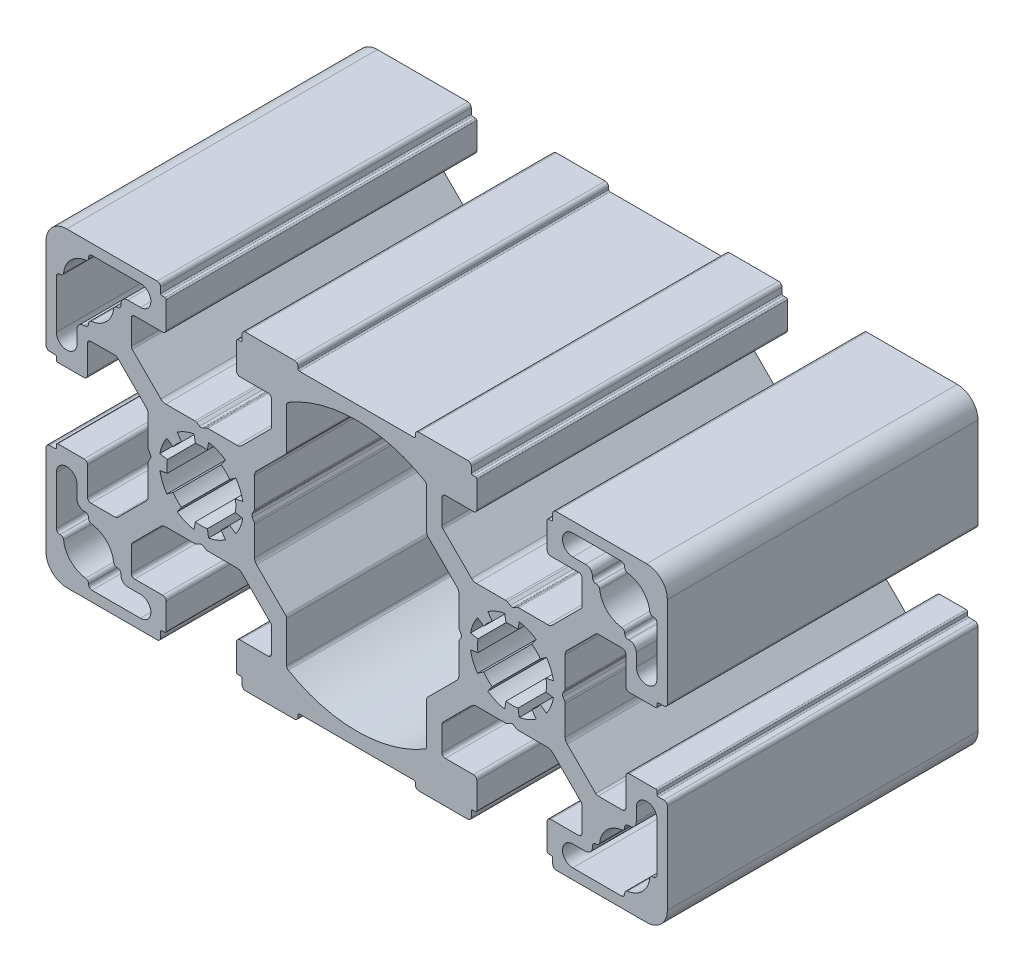
SolidWorks part; units mm, degrees
material "АД31Т ГОСТ 4784-97"
ref_plane "Спереди" through (0, 0, 0) normal (0, 0, 1) x (1, 0, 0)
ref_plane "Сверху" through (0, 0, 0) normal (0, 1, 0) x (1, 0, 0)
ref_plane "Справа" through (0, 0, 0) normal (1, 0, 0) x (0, 0, -1)
sketch "Эскиз1" plane through (0, 0, 0) normal (0, 0, 1) x (1, 0, 0)
  line L0 (-48.4414, 51.0481) -> (-48.4414, 44.0311)
  line L1 (-43.2664, 14.2231) -> (-36.2493, 14.2231)
  line L2 (-35.1419, 36.1522) -> (-35.1419, 40.3881)
  line L3 (-21.8414, 51.7231) -> (-17.7914, 51.7231)
  line L4 (-15.0914, 49.4623) -> (-15.0914, 45.6589)
  line L5 (-17.2012, 43.3419) -> (-15.2378, 45.3054)
  line L6 (-34.8271, 34.9731) -> (-35.0594, 34.5709)
  line L7 (-30.3093, 39.3189) -> (-30.9402, 40.2199)
  line L8 (-43.9414, 40.8231) -> (-43.9414, 44.8731)
  line L9 (-43.4414, 45.3731) -> (-39.9198, 45.3731)
  line L10 (-49.4414, 41.1231) -> (-48.6414, 41.1231)
  line L11 (-48.2414, 40.3231) -> (-44.4414, 40.3231)
  line L12 (-48.4414, 40.9231) -> (-48.4414, 40.5231)
  line L13 (-49.4414, 41.1231) -> (-48.6414, 41.1231)
  line L14 (-23.3456, 38.091) -> (-22.4445, 38.7219)
  line L15 (-23.3456, 38.091) -> (-22.4445, 38.7219)
  line L16 (-48.4414, 40.9231) -> (-48.4414, 40.5231)
  line L17 (-35.5602, 45.4633) -> (-33.3134, 43.2165)
  line L18 (-26.5123, 42.9236) -> (-22.2764, 42.9236)
  line L19 (-49.9414, 41.6231) -> (-49.9414, 54.7231)
  line L20 (-17.2914, 51.2231) -> (-17.2914, 47.7015)
  line L21 (-27.1914, 42.6089) -> (-26.7623, 42.8566)
  line L22 (11.9586, 18.7231) -> (7.9086, 18.7231)
  line L23 (-33.8414, 57.7231) -> (-46.9414, 57.7231)
  line L24 (-21.0414, 57.7231) -> (-13.9414, 57.7231)
  line L25 (-37.6815, 43.3419) -> (-39.5662, 45.2267)
  line L26 (-33.1414, 56.2231) -> (-32.7414, 56.2231)
  line L27 (-34.8271, 35.4731) -> (-35.0749, 35.9022)
  line L28 (-27.6914, 42.6089) -> (-28.1205, 42.8566)
  line L29 (-33.3414, 57.2231) -> (-33.3414, 56.4231)
  line L30 (-33.1414, 56.2231) -> (-32.7414, 56.2231)
  line L31 (-32.5414, 56.0231) -> (-32.5414, 52.2231)
  line L32 (-33.3414, 57.2231) -> (-33.3414, 56.4231)
  line L33 (-35.5602, 45.4633) -> (-37.4449, 47.348)
  line L34 (-33.0414, 51.7231) -> (-37.0914, 51.7231)
  line L35 (-37.6815, 43.3419) -> (-35.4347, 41.0952)
  line L36 (3.3586, 56.7231) -> (-13.2414, 56.7231)
  line L37 (-39.6466, 51.5481) -> (-39.5914, 51.5481)
  line L38 (-47.8861, 51.5481) -> (-47.9414, 51.5481)
  line L39 (-13.4414, 56.9231) -> (-13.4414, 57.2231)
  line L40 (-39.0914, 52.0481) -> (-39.0914, 52.2231)
  line L41 (-45.4414, 45.8731) -> (-45.4414, 44.0311)
  line L42 (-44.2664, 46.8731) -> (-44.4414, 46.8731)
  line L43 (-15.0914, 51.5901) -> (-15.0914, 49.4623)
  line L44 (-43.7664, 47.4284) -> (-43.7664, 47.3731)
  line L45 (38.5586, 19.3981) -> (38.5586, 26.4152)
  line L46 (-17.2012, 43.3419) -> (-19.448, 41.0952)
  line L47 (-27.1914, 42.6089) -> (-26.7891, 42.8411)
  line L48 (-28.3705, 42.9236) -> (-32.6063, 42.9236)
  line L49 (-21.8414, 51.7231) -> (-17.7914, 51.7231)
  line L50 (-19.3226, 45.4633) -> (-17.4378, 47.348)
  line L51 (-21.5414, 57.2231) -> (-21.5414, 56.4231)
  line L52 (-22.3414, 56.0231) -> (-22.3414, 52.2231)
  line L53 (-28.3705, 27.5226) -> (-32.6063, 27.5226)
  line L54 (-21.7414, 56.2231) -> (-22.1414, 56.2231)
  line L55 (-21.5414, 57.2231) -> (-21.5414, 56.4231)
  line L56 (-27.6914, 27.8374) -> (-28.1205, 27.5896)
  line L57 (-21.7414, 56.2231) -> (-22.1414, 56.2231)
  line L58 (-21.7414, 14.2231) -> (-22.1414, 14.2231)
  line L59 (-21.5414, 13.2231) -> (-21.5414, 14.0231)
  line L60 (-21.7414, 14.2231) -> (-22.1414, 14.2231)
  line L61 (-37.5914, 51.2231) -> (-37.5914, 47.7015)
  line L62 (-19.3226, 45.4633) -> (-21.5693, 43.2165)
  line L63 (-27.1914, 27.8374) -> (-26.7623, 27.5896)
  line L64 (-22.3414, 14.4231) -> (-22.3414, 18.2231)
  line L65 (-27.6914, 27.8374) -> (-28.0936, 27.6051)
  line L66 (-21.5414, 13.2231) -> (-21.5414, 14.0231)
  line L67 (-19.3226, 24.983) -> (-17.4378, 23.0982)
  line L68 (-21.8414, 18.7231) -> (-17.7914, 18.7231)
  line L69 (5.2086, 20.9839) -> (5.2086, 24.7873)
  line L70 (7.4086, 19.2231) -> (7.4086, 22.7447)
  line L71 (11.1586, 12.7231) -> (4.0586, 12.7231)
  line L72 (-28.3705, 42.9236) -> (-32.6063, 42.9236)
  line L73 (-24.5735, 39.3189) -> (-23.9426, 40.2199)
  line L74 (-19.7409, 36.1522) -> (-19.7409, 40.3881)
  line L75 (-26.5123, 27.5226) -> (-22.2764, 27.5226)
  line L76 (3.5586, 13.5231) -> (3.5586, 13.2231)
  line L77 (-33.0414, 18.7231) -> (-37.0914, 18.7231)
  line L78 (-43.7664, 14.7784) -> (-43.7664, 14.7231)
  line L79 (-23.3456, 32.3552) -> (-22.4445, 31.7243)
  line L80 (-24.5735, 31.1274) -> (-23.9426, 30.2263)
  line L81 (-38.0914, 17.2231) -> (-36.2493, 17.2231)
  line L82 (-23.3456, 32.3552) -> (-22.4445, 31.7243)
  line L83 (-24.5735, 31.1274) -> (-23.9426, 30.2263)
  line L84 (-26.5731, 30.2991) -> (-26.3821, 29.2158)
  line L85 (-26.5731, 30.2991) -> (-26.3821, 29.2158)
  line L86 (-28.3096, 30.2991) -> (-28.5006, 29.2158)
  line L87 (-31.5371, 32.3552) -> (-32.4382, 31.7243)
  line L88 (-28.3096, 30.2991) -> (-28.5006, 29.2158)
  line L89 (-31.5371, 32.3552) -> (-32.4382, 31.7243)
  line L90 (5.2086, 18.8562) -> (5.2086, 20.9839)
  line L91 (-24.5735, 31.1274) -> (-23.9426, 30.2263)
  line L92 (-28.3705, 27.5226) -> (-32.6063, 27.5226)
  line L93 (-17.2914, 19.2231) -> (-17.2914, 22.7447)
  line L94 (-17.2012, 27.1043) -> (-15.2378, 25.1409)
  line L95 (-15.0914, 20.9839) -> (-15.0914, 24.7873)
  line L96 (-21.8414, 18.7231) -> (-17.7914, 18.7231)
  line L97 (20.4265, 31.1274) -> (21.0574, 30.2263)
  line L98 (34.0586, 29.6231) -> (34.0586, 25.5731)
  line L99 (-19.3226, 24.983) -> (-21.5693, 27.2297)
  line L100 (-34.8271, 34.9731) -> (-35.0749, 34.544)
  line L101 (-37.5914, 19.2231) -> (-37.5914, 22.7447)
  line L102 (20.4265, 31.1274) -> (21.0574, 30.2263)
  line L103 (33.5586, 25.0731) -> (30.0371, 25.0731)
  line L104 (-17.2012, 27.1043) -> (-15.3165, 25.2196)
  line L105 (39.5586, 29.3231) -> (38.7586, 29.3231)
  line L106 (-19.7409, 34.294) -> (-19.7409, 30.0582)
  line L107 (38.3586, 30.1231) -> (34.5586, 30.1231)
  line L108 (38.5586, 29.5231) -> (38.5586, 29.9231)
  line L109 (-20.0556, 35.4731) -> (-19.8234, 35.8754)
  line L110 (39.5586, 29.3231) -> (38.7586, 29.3231)
  line L111 (13.4629, 32.3552) -> (12.5618, 31.7243)
  line L112 (-35.1419, 34.294) -> (-35.1419, 30.0582)
  line L113 (13.4629, 32.3552) -> (12.5618, 31.7243)
  line L114 (13.4629, 32.3552) -> (12.5618, 31.7243)
  line L115 (-28.3705, 27.5226) -> (-32.6063, 27.5226)
  line L116 (-27.1914, 27.8374) -> (-26.7891, 27.6051)
  line L117 (-17.2012, 27.1043) -> (-19.448, 29.3511)
  line L118 (38.5586, 29.5231) -> (38.5586, 29.9231)
  line L119 (-43.7664, 23.0179) -> (-43.7664, 23.0731)
  line L120 (-20.0556, 34.9731) -> (-19.8079, 34.544)
  line L121 (25.6774, 24.983) -> (23.4307, 27.2297)
  line L122 (-44.2664, 23.5731) -> (-44.4414, 23.5731)
  line L123 (-45.4414, 24.5731) -> (-45.4414, 26.4152)
  line L124 (-39.0914, 18.3981) -> (-39.0914, 18.2231)
  line L125 (9.8581, 36.1522) -> (9.8581, 40.3881)
  line L126 (-47.8861, 18.8981) -> (-47.9414, 18.8981)
  line L127 (-31.5371, 38.091) -> (-32.4382, 38.7219)
  line L128 (-28.3096, 40.1472) -> (-28.5006, 41.2304)
  line L129 (-26.5731, 40.1472) -> (-26.3821, 41.2304)
  line L130 (-38.0914, 53.2231) -> (-36.2493, 53.2231)
  line L131 (-32.3654, 34.3549) -> (-33.4487, 34.1639)
  line L132 (-32.3654, 36.0914) -> (-33.4487, 36.2824)
  line L133 (-26.5731, 30.2991) -> (-26.3821, 29.2158)
  line L134 (-28.3096, 30.2991) -> (-28.5006, 29.2158)
  line L135 (-30.3093, 31.1274) -> (-30.9402, 30.2263)
  line L136 (-31.5371, 32.3552) -> (-32.4382, 31.7243)
  line L137 (-32.3654, 34.3549) -> (-33.4487, 34.1639)
  line L138 (-32.3654, 36.0914) -> (-33.4487, 36.2824)
  line L139 (-24.5735, 39.3189) -> (-23.9426, 40.2199)
  line L140 (-23.3456, 38.091) -> (-22.4445, 38.7219)
  line L141 (-22.5173, 36.0914) -> (-21.434, 36.2824)
  line L142 (-22.5173, 34.3549) -> (-21.434, 34.1639)
  line L143 (-23.3456, 32.3552) -> (-22.4445, 31.7243)
  line L144 (-24.5735, 31.1274) -> (-23.9426, 30.2263)
  line L145 (-43.7664, 55.6679) -> (-43.7664, 55.7231)
  line L146 (-39.6466, 18.8981) -> (-39.5914, 18.8981)
  line L147 (-33.0414, 51.7231) -> (-37.0914, 51.7231)
  line L148 (-43.2664, 56.2231) -> (-36.2493, 56.2231)
  line L149 (16.6295, 27.5226) -> (12.3937, 27.5226)
  line L150 (-37.6815, 27.1043) -> (-35.4347, 29.3511)
  line L151 (-33.0414, 18.7231) -> (-37.0914, 18.7231)
  line L152 (-35.5602, 24.983) -> (-37.4449, 23.0982)
  line L153 (-33.3414, 13.2231) -> (-33.3414, 14.0231)
  line L154 (-32.5414, 14.4231) -> (-32.5414, 18.2231)
  line L155 (-33.1414, 14.2231) -> (-32.7414, 14.2231)
  line L156 (-33.3414, 13.2231) -> (-33.3414, 14.0231)
  line L157 (-27.6914, 27.8374) -> (-28.1205, 27.5896)
  line L158 (-33.1414, 14.2231) -> (-32.7414, 14.2231)
  line L159 (-37.6815, 27.1043) -> (-39.5662, 25.2196)
  line L160 (40.0586, 28.8231) -> (40.0586, 15.7231)
  line L161 (-33.8414, 12.7231) -> (-46.9414, 12.7231)
  line L162 (10.1729, 35.4731) -> (9.9251, 35.9022)
  line L163 (-27.1914, 27.8374) -> (-26.7623, 27.5896)
  line L164 (17.3086, 27.8374) -> (16.8795, 27.5896)
  line L165 (-20.0556, 35.4731) -> (-19.8079, 35.9022)
  line L166 (-49.9414, 28.8231) -> (-49.9414, 15.7231)
  line L167 (-26.5123, 27.5226) -> (-22.2764, 27.5226)
  line L168 (-19.7409, 36.1522) -> (-19.7409, 40.3881)
  line L169 (-35.5602, 24.983) -> (-33.3134, 27.2297)
  line L170 (-48.4414, 29.5231) -> (-48.4414, 29.9231)
  line L171 (-23.3456, 32.3552) -> (-22.4445, 31.7243)
  line L172 (-23.3456, 32.3552) -> (-22.4445, 31.7243)
  line L173 (-23.3456, 32.3552) -> (-22.4445, 31.7243)
  line L174 (-49.4414, 29.3231) -> (-48.6414, 29.3231)
  line L175 (-48.4414, 29.5231) -> (-48.4414, 29.9231)
  line L176 (-48.2414, 30.1231) -> (-44.4414, 30.1231)
  line L177 (-49.4414, 29.3231) -> (-48.6414, 29.3231)
  line L178 (-43.4414, 25.0731) -> (-39.9198, 25.0731)
  line L179 (-30.3093, 31.1274) -> (-30.9402, 30.2263)
  line L180 (-43.9414, 29.6231) -> (-43.9414, 25.5731)
  line L181 (-30.3093, 31.1274) -> (-30.9402, 30.2263)
  line L182 (23.9586, 12.7231) -> (37.0586, 12.7231)
  line L183 (27.7988, 27.1043) -> (29.6835, 25.2196)
  line L184 (23.2586, 14.2231) -> (22.8586, 14.2231)
  line L185 (17.8086, 27.8374) -> (18.2377, 27.5896)
  line L186 (-48.4414, 19.3981) -> (-48.4414, 26.4152)
  line L187 (23.4586, 13.2231) -> (23.4586, 14.0231)
  line L188 (23.2586, 14.2231) -> (22.8586, 14.2231)
  line L189 (22.6586, 14.4231) -> (22.6586, 18.2231)
  line L190 (23.4586, 13.2231) -> (23.4586, 14.0231)
  line L191 (25.6774, 24.983) -> (27.5622, 23.0982)
  line L192 (23.1586, 18.7231) -> (27.2086, 18.7231)
  line L193 (27.7988, 27.1043) -> (25.552, 29.3511)
  line L194 (33.3836, 56.2231) -> (26.3666, 56.2231)
  line L195 (23.1586, 51.7231) -> (27.2086, 51.7231)
  line L196 (29.7639, 18.8981) -> (29.7086, 18.8981)
  line L197 (33.8836, 55.6679) -> (33.8836, 55.7231)
  line L198 (14.6907, 31.1274) -> (14.0598, 30.2263)
  line L199 (13.4629, 32.3552) -> (12.5618, 31.7243)
  line L200 (12.6346, 34.3549) -> (11.5513, 34.1639)
  line L201 (12.6346, 36.0914) -> (11.5513, 36.2824)
  line L202 (13.4629, 38.091) -> (12.5618, 38.7219)
  line L203 (14.6907, 39.3189) -> (14.0598, 40.2199)
  line L204 (22.4827, 36.0914) -> (23.566, 36.2824)
  line L205 (22.4827, 34.3549) -> (23.566, 34.1639)
  line L206 (21.6544, 32.3552) -> (22.5555, 31.7243)
  line L207 (20.4265, 31.1274) -> (21.0574, 30.2263)
  line L208 (18.4269, 30.2991) -> (18.6179, 29.2158)
  line L209 (16.6904, 30.2991) -> (16.4994, 29.2158)
  line L210 (22.4827, 36.0914) -> (23.566, 36.2824)
  line L211 (22.4827, 34.3549) -> (23.566, 34.1639)
  line L212 (28.2086, 53.2231) -> (26.3666, 53.2231)
  line L213 (16.6904, 40.1472) -> (16.4994, 41.2304)
  line L214 (18.4269, 40.1472) -> (18.6179, 41.2304)
  line L215 (21.6544, 38.091) -> (22.5555, 38.7219)
  line L216 (38.0034, 18.8981) -> (38.0586, 18.8981)
  line L217 (29.2086, 18.3981) -> (29.2086, 18.2231)
  line L218 (35.5586, 24.5731) -> (35.5586, 26.4152)
  line L219 (34.3836, 23.5731) -> (34.5586, 23.5731)
  line L220 (10.1729, 34.9731) -> (9.9251, 34.544)
  line L221 (33.8836, 23.0179) -> (33.8836, 23.0731)
  line L222 (7.3185, 27.1043) -> (9.5653, 29.3511)
  line L223 (17.3086, 27.8374) -> (16.9064, 27.6051)
  line L224 (18.4877, 27.5226) -> (22.7236, 27.5226)
  line L225 (25.2591, 34.294) -> (25.2591, 30.0582)
  line L226 (10.1729, 35.4731) -> (9.9406, 35.8754)
  line L227 (9.8581, 34.294) -> (9.8581, 30.0582)
  line L228 (7.3185, 27.1043) -> (5.4338, 25.2196)
  line L229 (27.7086, 19.2231) -> (27.7086, 22.7447)
  line L230 (24.9444, 34.9731) -> (25.1921, 34.544)
  line L231 (9.4398, 24.983) -> (11.6866, 27.2297)
  line L232 (11.9586, 18.7231) -> (7.9086, 18.7231)
  line L233 (5.2086, 20.9839) -> (5.2086, 24.7873)
  line L234 (7.3185, 27.1043) -> (5.3551, 25.1409)
  line L235 (7.4086, 19.2231) -> (7.4086, 22.7447)
  line L236 (18.4877, 27.5226) -> (22.7236, 27.5226)
  line L237 (14.6907, 31.1274) -> (14.0598, 30.2263)
  line L238 (21.6544, 32.3552) -> (22.5555, 31.7243)
  line L239 (18.4269, 30.2991) -> (18.6179, 29.2158)
  line L240 (21.6544, 32.3552) -> (22.5555, 31.7243)
  line L241 (18.4269, 30.2991) -> (18.6179, 29.2158)
  line L242 (16.6904, 30.2991) -> (16.4994, 29.2158)
  line L243 (16.6904, 30.2991) -> (16.4994, 29.2158)
  line L244 (14.6907, 31.1274) -> (14.0598, 30.2263)
  line L245 (13.4629, 32.3552) -> (12.5618, 31.7243)
  line L246 (28.2086, 17.2231) -> (26.3666, 17.2231)
  line L247 (14.6907, 31.1274) -> (14.0598, 30.2263)
  line L248 (13.4629, 32.3552) -> (12.5618, 31.7243)
  line L249 (33.8836, 14.7784) -> (33.8836, 14.7231)
  line L250 (23.1586, 18.7231) -> (27.2086, 18.7231)
  line L251 (11.9586, 18.7231) -> (7.9086, 18.7231)
  line L252 (16.6295, 27.5226) -> (12.3937, 27.5226)
  line L253 (9.8581, 36.1522) -> (9.8581, 40.3881)
  line L254 (14.6907, 39.3189) -> (14.0598, 40.2199)
  line L255 (18.4877, 42.9236) -> (22.7236, 42.9236)
  line L256 (9.4398, 24.983) -> (7.5551, 23.0982)
  line L257 (11.6586, 13.2231) -> (11.6586, 14.0231)
  line L258 (11.9586, 18.7231) -> (7.9086, 18.7231)
  line L259 (9.4398, 24.983) -> (7.5551, 23.0982)
  line L260 (11.6586, 13.2231) -> (11.6586, 14.0231)
  line L261 (17.8086, 27.8374) -> (18.2109, 27.6051)
  line L262 (12.4586, 14.4231) -> (12.4586, 18.2231)
  line L263 (17.3086, 27.8374) -> (16.8795, 27.5896)
  line L264 (9.4398, 45.4633) -> (11.6866, 43.2165)
  line L265 (27.7086, 51.2231) -> (27.7086, 47.7015)
  line L266 (11.8586, 14.2231) -> (12.2586, 14.2231)
  line L267 (11.6586, 13.2231) -> (11.6586, 14.0231)
  line L268 (11.8586, 14.2231) -> (12.2586, 14.2231)
  line L269 (11.8586, 56.2231) -> (12.2586, 56.2231)
  line L270 (17.8086, 27.8374) -> (18.2377, 27.5896)
  line L271 (11.6586, 57.2231) -> (11.6586, 56.4231)
  line L272 (11.8586, 56.2231) -> (12.2586, 56.2231)
  line L273 (18.4877, 27.5226) -> (22.7236, 27.5226)
  line L274 (12.4586, 56.0231) -> (12.4586, 52.2231)
  line L275 (11.6586, 57.2231) -> (11.6586, 56.4231)
  line L276 (9.4398, 45.4633) -> (7.5551, 47.348)
  line L277 (11.9586, 51.7231) -> (7.9086, 51.7231)
  line L278 (18.4877, 42.9236) -> (22.7236, 42.9236)
  line L279 (17.3086, 42.6089) -> (16.9064, 42.8411)
  line L280 (7.3185, 43.3419) -> (9.5653, 41.0952)
  line L281 (33.8836, 47.4284) -> (33.8836, 47.3731)
  line L282 (5.2086, 51.5901) -> (5.2086, 49.4623)
  line L283 (34.3836, 46.8731) -> (34.5586, 46.8731)
  line L284 (35.5586, 45.8731) -> (35.5586, 44.0311)
  line L285 (29.2086, 52.0481) -> (29.2086, 52.2231)
  line L286 (3.5586, 56.9231) -> (3.5586, 57.2231)
  line L287 (38.0034, 51.5481) -> (38.0586, 51.5481)
  line L288 (29.7639, 51.5481) -> (29.7086, 51.5481)
  line L289 (27.7988, 43.3419) -> (25.552, 41.0952)
  line L290 (23.1586, 51.7231) -> (27.2086, 51.7231)
  line L291 (25.6774, 45.4633) -> (27.5622, 47.348)
  line L292 (23.4586, 57.2231) -> (23.4586, 56.4231)
  line L293 (22.6586, 56.0231) -> (22.6586, 52.2231)
  line L294 (23.2586, 56.2231) -> (22.8586, 56.2231)
  line L295 (23.4586, 57.2231) -> (23.4586, 56.4231)
  line L296 (17.8086, 42.6089) -> (18.2377, 42.8566)
  line L297 (24.9444, 35.4731) -> (25.1921, 35.9022)
  line L298 (23.2586, 56.2231) -> (22.8586, 56.2231)
  line L299 (27.7988, 43.3419) -> (29.6835, 45.2267)
  line L300 (11.1586, 57.7231) -> (4.0586, 57.7231)
  line L301 (23.9586, 57.7231) -> (37.0586, 57.7231)
  line L302 (17.3086, 42.6089) -> (16.8795, 42.8566)
  line L303 (7.4086, 51.2231) -> (7.4086, 47.7015)
  line L304 (40.0586, 41.6231) -> (40.0586, 54.7231)
  line L305 (16.6295, 42.9236) -> (12.3937, 42.9236)
  line L306 (25.6774, 45.4633) -> (23.4307, 43.2165)
  line L307 (38.5586, 40.9231) -> (38.5586, 40.5231)
  line L308 (13.4629, 38.091) -> (12.5618, 38.7219)
  line L309 (13.4629, 38.091) -> (12.5618, 38.7219)
  line L310 (39.5586, 41.1231) -> (38.7586, 41.1231)
  line L311 (38.5586, 40.9231) -> (38.5586, 40.5231)
  line L312 (38.3586, 40.3231) -> (34.5586, 40.3231)
  line L313 (39.5586, 41.1231) -> (38.7586, 41.1231)
  line L314 (33.5586, 45.3731) -> (30.0371, 45.3731)
  line L315 (34.0586, 40.8231) -> (34.0586, 44.8731)
  line L316 (20.4265, 39.3189) -> (21.0574, 40.2199)
  line L317 (24.9444, 34.9731) -> (25.1766, 34.5709)
  line L318 (7.3185, 43.3419) -> (5.3551, 45.3054)
  line L319 (5.2086, 49.4623) -> (5.2086, 45.6589)
  line L320 (11.9586, 51.7231) -> (7.9086, 51.7231)
  line L321 (25.2591, 36.1522) -> (25.2591, 40.3881)
  line L322 (33.3836, 14.2231) -> (26.3666, 14.2231)
  line L323 (38.5586, 51.0481) -> (38.5586, 44.0311)
  line L325 (12.4586, 14.4231) -> (12.4586, 18.2231)
  line L326 (11.8586, 14.2231) -> (12.2586, 14.2231)
  line L327 (11.6586, 13.2231) -> (11.6586, 14.0231)
  line L328 (11.8586, 14.2231) -> (12.2586, 14.2231)
  line L329 (-21.7414, 14.2231) -> (-22.1414, 14.2231)
  line L330 (-21.5414, 13.2231) -> (-21.5414, 14.0231)
  line L331 (-21.7414, 14.2231) -> (-22.1414, 14.2231)
  line L332 (-22.3414, 14.4231) -> (-22.3414, 18.2231)
  line L333 (-21.5414, 13.2231) -> (-21.5414, 14.0231)
  line L334 (-19.3226, 24.983) -> (-17.4378, 23.0982)
  line L335 (-21.8414, 18.7231) -> (-17.7914, 18.7231)
  line L336 (-15.0914, 18.8562) -> (-15.0914, 20.9839)
  line L337 (-13.4414, 13.5231) -> (-13.4414, 13.2231)
  line L338 (3.3586, 13.7231) -> (-13.2414, 13.7231)
  line L339 (-21.0414, 12.7231) -> (-13.9414, 12.7231)
  line L340 (-17.2914, 19.2231) -> (-17.2914, 22.7447)
  line L341 (-15.0914, 20.9839) -> (-15.0914, 24.7873)
  line L342 (-21.8414, 18.7231) -> (-17.7914, 18.7231)
  arc A0 (-30.3093, 39.3189) -> (-31.5371, 38.091) centre (-27.4414, 35.2231) ccw
  arc A1 (-32.4382, 38.7219) -> (-33.4487, 36.2824) centre (-27.4414, 35.2231) ccw
  arc A2 (-46.9414, 57.7231) -> (-49.9414, 54.7231) centre (-46.9414, 54.7231) ccw
  arc A3 (-39.5662, 45.2267) -> (-39.9198, 45.3731) centre (-39.9198, 44.8731) ccw
  arc A4 (-43.4414, 45.3731) -> (-43.9414, 44.8731) centre (-43.4414, 44.8731) ccw
  arc A5 (-44.4414, 40.3231) -> (-43.9414, 40.8231) centre (-44.4414, 40.8231) ccw
  arc A6 (-49.9414, 41.6231) -> (-49.4414, 41.1231) centre (-49.4414, 41.6231) ccw
  arc A7 (-48.2414, 40.3231) -> (-48.4414, 40.5231) centre (-48.2414, 40.5231) cw
  arc A8 (-48.6414, 41.1231) -> (-48.4414, 40.9231) centre (-48.6414, 40.9231) cw
  arc A9 (-35.4347, 41.0952) -> (-35.1419, 40.3881) centre (-36.1419, 40.3881) cw
  arc A10 (-17.2914, 51.2231) -> (-17.7914, 51.7231) centre (-17.7914, 51.2231) ccw
  arc A11 (-15.2378, 45.3054) -> (-15.0914, 45.6589) centre (-15.5914, 45.6589) ccw
  arc A12 (4.9626, 52.0208) -> (5.2086, 51.5901) centre (4.7086, 51.5901) cw
  arc A13 (-13.4414, 57.2231) -> (-13.9414, 57.7231) centre (-13.9414, 57.2231) ccw
  arc A14 (-13.2414, 56.7231) -> (-13.4414, 56.9231) centre (-13.2414, 56.9231) cw
  arc A15 (-21.5414, 14.0231) -> (-21.7414, 14.2231) centre (-21.7414, 14.0231) ccw
  arc A16 (-35.0749, 34.544) -> (-35.1419, 34.294) centre (-34.6419, 34.294) ccw
  arc A17 (-33.3414, 56.4231) -> (-33.1414, 56.2231) centre (-33.1414, 56.4231) ccw
  arc A18 (-34.8271, 34.9731) -> (-34.8271, 35.4731) centre (-35.2601, 35.2231) ccw
  arc A19 (-49.9414, 41.6231) -> (-49.4414, 41.1231) centre (-49.4414, 41.6231) ccw
  arc A20 (-48.6414, 41.1231) -> (-48.4414, 40.9231) centre (-48.6414, 40.9231) cw
  arc A21 (-33.8414, 57.7231) -> (-33.3414, 57.2231) centre (-33.8414, 57.2231) cw
  arc A22 (-28.1205, 42.8566) -> (-28.3705, 42.9236) centre (-28.3705, 42.4236) ccw
  arc A23 (-21.0414, 12.7231) -> (-21.5414, 13.2231) centre (-21.0414, 13.2231) cw
  arc A24 (-27.1914, 42.6089) -> (-27.6914, 42.6089) centre (-27.4414, 43.0419) cw
  arc A25 (-33.3414, 56.4231) -> (-33.1414, 56.2231) centre (-33.1414, 56.4231) ccw
  arc A26 (-32.5414, 56.0231) -> (-32.7414, 56.2231) centre (-32.7414, 56.0231) ccw
  arc A27 (-33.8414, 57.7231) -> (-33.3414, 57.2231) centre (-33.8414, 57.2231) cw
  arc A28 (-32.5414, 52.2231) -> (-33.0414, 51.7231) centre (-33.0414, 52.2231) cw
  arc A29 (-37.5914, 51.2231) -> (-37.0914, 51.7231) centre (-37.0914, 51.2231) cw
  arc A30 (-33.3134, 43.2165) -> (-32.6063, 42.9236) centre (-32.6063, 43.9236) ccw
  arc A31 (-43.3266, 47.9247) -> (-40.143, 51.1084) centre (-43.7664, 51.5481) ccw
  arc A32 (-48.4414, 44.0311) -> (-45.4414, 44.0311) centre (-46.9414, 44.0311) ccw
  arc A33 (-44.4414, 46.8731) -> (-45.4414, 45.8731) centre (-44.4414, 45.8731) ccw
  arc A34 (-47.9414, 51.5481) -> (-48.4414, 51.0481) centre (-47.9414, 51.0481) ccw
  arc A35 (-47.8861, 51.5481) -> (-47.3898, 51.9879) centre (-47.8861, 52.0481) ccw
  arc A36 (-43.7664, 47.4284) -> (-43.3266, 47.9247) centre (-43.2664, 47.4284) cw
  arc A37 (-21.5414, 14.0231) -> (-21.7414, 14.2231) centre (-21.7414, 14.0231) ccw
  arc A38 (-22.3414, 14.4231) -> (-22.1414, 14.2231) centre (-22.1414, 14.4231) ccw
  arc A39 (-21.0414, 12.7231) -> (-21.5414, 13.2231) centre (-21.0414, 13.2231) cw
  arc A40 (-17.4378, 47.348) -> (-17.2914, 47.7015) centre (-17.7914, 47.7015) ccw
  arc A41 (-22.3414, 18.2231) -> (-21.8414, 18.7231) centre (-21.8414, 18.2231) cw
  arc A42 (-17.2914, 19.2231) -> (-17.7914, 18.7231) centre (-17.7914, 19.2231) cw
  arc A43 (-26.7623, 42.8566) -> (-26.5123, 42.9236) centre (-26.5123, 42.4236) cw
  arc A44 (-37.4449, 47.348) -> (-37.5914, 47.7015) centre (-37.0914, 47.7015) cw
  arc A45 (-17.4378, 23.0982) -> (-17.2914, 22.7447) centre (-17.7914, 22.7447) cw
  arc A46 (4.9626, 18.4254) -> (-14.8453, 18.4254) centre (-4.9414, 35.2231) cw
  arc A47 (7.4086, 19.2231) -> (7.9086, 18.7231) centre (7.9086, 19.2231) ccw
  arc A48 (-26.7623, 27.5896) -> (-26.5123, 27.5226) centre (-26.5123, 28.0226) ccw
  arc A49 (5.3551, 25.1409) -> (5.2086, 24.7873) centre (5.7086, 24.7873) ccw
  arc A50 (-21.5693, 43.2165) -> (-22.2764, 42.9236) centre (-22.2764, 43.9236) cw
  arc A51 (-27.6914, 27.8374) -> (-27.1914, 27.8374) centre (-27.4414, 27.4044) cw
  arc A52 (-17.2914, 51.2231) -> (-17.7914, 51.7231) centre (-17.7914, 51.2231) ccw
  arc A53 (-22.3414, 52.2231) -> (-21.8414, 51.7231) centre (-21.8414, 52.2231) ccw
  arc A54 (-21.0414, 57.7231) -> (-21.5414, 57.2231) centre (-21.0414, 57.2231) ccw
  arc A55 (-22.3414, 56.0231) -> (-22.1414, 56.2231) centre (-22.1414, 56.0231) cw
  arc A56 (-21.5414, 56.4231) -> (-21.7414, 56.2231) centre (-21.7414, 56.4231) cw
  arc A57 (-21.0414, 57.7231) -> (-21.5414, 57.2231) centre (-21.0414, 57.2231) ccw
  arc A58 (-28.1205, 27.5896) -> (-28.3705, 27.5226) centre (-28.3705, 28.0226) cw
  arc A59 (-15.2378, 25.1409) -> (-15.0914, 24.7873) centre (-15.5914, 24.7873) cw
  arc A60 (-17.2914, 19.2231) -> (-17.7914, 18.7231) centre (-17.7914, 19.2231) cw
  arc A61 (-21.5414, 56.4231) -> (-21.7414, 56.2231) centre (-21.7414, 56.4231) cw
  arc A62 (-19.448, 41.0952) -> (-19.7409, 40.3881) centre (-18.7409, 40.3881) ccw
  arc A63 (20.4265, 31.1274) -> (21.6544, 32.3552) centre (17.5586, 35.2231) ccw
  arc A64 (37.0586, 12.7231) -> (40.0586, 15.7231) centre (37.0586, 15.7231) ccw
  arc A65 (29.6835, 25.2196) -> (30.0371, 25.0731) centre (30.0371, 25.5731) ccw
  arc A66 (33.5586, 25.0731) -> (34.0586, 25.5731) centre (33.5586, 25.5731) ccw
  arc A67 (-19.8079, 35.9022) -> (-19.7409, 36.1522) centre (-20.2409, 36.1522) ccw
  arc A68 (34.5586, 30.1231) -> (34.0586, 29.6231) centre (34.5586, 29.6231) ccw
  arc A69 (40.0586, 28.8231) -> (39.5586, 29.3231) centre (39.5586, 28.8231) ccw
  arc A70 (38.3586, 30.1231) -> (38.5586, 29.9231) centre (38.3586, 29.9231) cw
  arc A71 (-22.4445, 38.7219) -> (-21.434, 36.2824) centre (-27.4414, 35.2231) cw
  arc A72 (-20.0556, 35.4731) -> (-20.0556, 34.9731) centre (-19.6226, 35.2231) ccw
  arc A73 (-24.5735, 39.3189) -> (-23.3456, 38.091) centre (-27.4414, 35.2231) cw
  arc A74 (-37.5914, 19.2231) -> (-37.0914, 18.7231) centre (-37.0914, 19.2231) ccw
  arc A75 (-36.2493, 14.2231) -> (-36.2493, 17.2231) centre (-36.2493, 15.7231) ccw
  arc A76 (-39.0914, 18.2231) -> (-38.0914, 17.2231) centre (-38.0914, 18.2231) ccw
  arc A77 (-43.7664, 14.7231) -> (-43.2664, 14.2231) centre (-43.2664, 14.7231) ccw
  arc A78 (-43.7664, 14.7784) -> (-44.2061, 15.2747) centre (-44.2664, 14.7784) ccw
  arc A79 (-39.6466, 18.8981) -> (-40.143, 19.3379) centre (-39.6466, 19.3981) cw
  arc A80 (-39.5914, 18.8981) -> (-39.0914, 18.3981) centre (-39.5914, 18.3981) cw
  arc A81 (-44.2061, 15.2747) -> (-47.3898, 18.4584) centre (-43.7664, 18.8981) cw
  arc A82 (-43.7664, 23.0731) -> (-44.2664, 23.5731) centre (-44.2664, 23.0731) ccw
  arc A83 (-46.9414, 12.7231) -> (-49.9414, 15.7231) centre (-46.9414, 15.7231) cw
  arc A84 (-23.3456, 32.3552) -> (-24.5735, 31.1274) centre (-27.4414, 35.2231) cw
  arc A85 (-23.9426, 30.2263) -> (-26.3821, 29.2158) centre (-27.4414, 35.2231) cw
  arc A86 (-26.5731, 30.2991) -> (-28.3096, 30.2991) centre (-27.4414, 35.2231) cw
  arc A87 (-28.5006, 29.2158) -> (-30.9402, 30.2263) centre (-27.4414, 35.2231) cw
  arc A88 (-23.9426, 30.2263) -> (-26.3821, 29.2158) centre (-27.4414, 35.2231) cw
  arc A89 (-26.5731, 30.2991) -> (-28.3096, 30.2991) centre (-27.4414, 35.2231) cw
  arc A90 (-28.5006, 29.2158) -> (-30.9402, 30.2263) centre (-27.4414, 35.2231) cw
  arc A91 (-24.5735, 31.1274) -> (-23.3456, 32.3552) centre (-27.4414, 35.2231) ccw
  arc A92 (-19.8079, 34.544) -> (-19.7409, 34.294) centre (-20.2409, 34.294) cw
  arc A93 (38.7586, 29.3231) -> (38.5586, 29.5231) centre (38.7586, 29.5231) cw
  arc A94 (25.552, 29.3511) -> (25.2591, 30.0582) centre (26.2591, 30.0582) cw
  arc A95 (23.4586, 14.0231) -> (23.2586, 14.2231) centre (23.2586, 14.0231) ccw
  arc A96 (40.0586, 28.8231) -> (39.5586, 29.3231) centre (39.5586, 28.8231) ccw
  arc A97 (38.7586, 29.3231) -> (38.5586, 29.5231) centre (38.7586, 29.5231) cw
  arc A98 (23.9586, 12.7231) -> (23.4586, 13.2231) centre (23.9586, 13.2231) cw
  arc A99 (18.2377, 27.5896) -> (18.4877, 27.5226) centre (18.4877, 28.0226) ccw
  arc A100 (-19.448, 29.3511) -> (-19.7409, 30.0582) centre (-18.7409, 30.0582) cw
  arc A101 (17.3086, 27.8374) -> (17.8086, 27.8374) centre (17.5586, 27.4044) cw
  arc A102 (-35.0749, 35.9022) -> (-35.1419, 36.1522) centre (-34.6419, 36.1522) cw
  arc A103 (23.4586, 14.0231) -> (23.2586, 14.2231) centre (23.2586, 14.0231) ccw
  arc A104 (22.6586, 14.4231) -> (22.8586, 14.2231) centre (22.8586, 14.4231) ccw
  arc A105 (23.9586, 12.7231) -> (23.4586, 13.2231) centre (23.9586, 13.2231) cw
  arc A106 (22.6586, 18.2231) -> (23.1586, 18.7231) centre (23.1586, 18.2231) cw
  arc A107 (27.7086, 19.2231) -> (27.2086, 18.7231) centre (27.2086, 19.2231) cw
  arc A108 (23.4307, 27.2297) -> (22.7236, 27.5226) centre (22.7236, 26.5226) ccw
  arc A109 (33.4439, 22.5215) -> (30.2602, 19.3379) centre (33.8836, 18.8981) ccw
  arc A110 (38.5586, 26.4152) -> (35.5586, 26.4152) centre (37.0586, 26.4152) ccw
  arc A111 (-21.5693, 27.2297) -> (-22.2764, 27.5226) centre (-22.2764, 26.5226) ccw
  arc A112 (34.5586, 23.5731) -> (35.5586, 24.5731) centre (34.5586, 24.5731) ccw
  arc A113 (38.0586, 18.8981) -> (38.5586, 19.3981) centre (38.0586, 19.3981) ccw
  arc A114 (-28.5006, 41.2304) -> (-30.9402, 40.2199) centre (-27.4414, 35.2231) ccw
  arc A115 (-26.5731, 40.1472) -> (-28.3096, 40.1472) centre (-27.4414, 35.2231) ccw
  arc A116 (-23.9426, 40.2199) -> (-26.3821, 41.2304) centre (-27.4414, 35.2231) ccw
  arc A117 (-23.3456, 38.091) -> (-24.5735, 39.3189) centre (-27.4414, 35.2231) ccw
  arc A118 (-22.5173, 34.3549) -> (-22.5173, 36.0914) centre (-27.4414, 35.2231) ccw
  arc A119 (-21.434, 36.2824) -> (-22.4445, 38.7219) centre (-27.4414, 35.2231) ccw
  arc A120 (-24.5735, 31.1274) -> (-23.3456, 32.3552) centre (-27.4414, 35.2231) ccw
  arc A121 (-22.4445, 31.7243) -> (-21.434, 34.1639) centre (-27.4414, 35.2231) ccw
  arc A122 (-28.3096, 30.2991) -> (-26.5731, 30.2991) centre (-27.4414, 35.2231) ccw
  arc A123 (-26.3821, 29.2158) -> (-23.9426, 30.2263) centre (-27.4414, 35.2231) ccw
  arc A124 (-31.5371, 32.3552) -> (-30.3093, 31.1274) centre (-27.4414, 35.2231) ccw
  arc A125 (-30.9402, 30.2263) -> (-28.5006, 29.2158) centre (-27.4414, 35.2231) ccw
  arc A126 (-32.3654, 36.0914) -> (-32.3654, 34.3549) centre (-27.4414, 35.2231) ccw
  arc A127 (-33.4487, 34.1639) -> (-32.4382, 31.7243) centre (-27.4414, 35.2231) ccw
  arc A128 (-46.9414, 57.7231) -> (-49.9414, 54.7231) centre (-46.9414, 54.7231) ccw
  arc A129 (-43.7664, 47.3731) -> (-44.2664, 46.8731) centre (-44.2664, 47.3731) cw
  arc A130 (-44.2061, 55.1715) -> (-47.3898, 51.9879) centre (-43.7664, 51.5481) ccw
  arc A131 (-39.5914, 51.5481) -> (-39.0914, 52.0481) centre (-39.5914, 52.0481) ccw
  arc A132 (-39.6466, 51.5481) -> (-40.143, 51.1084) centre (-39.6466, 51.0481) ccw
  arc A133 (-43.7664, 55.6679) -> (-44.2061, 55.1715) centre (-44.2664, 55.6679) cw
  arc A134 (-43.7664, 55.7231) -> (-43.2664, 56.2231) centre (-43.2664, 55.7231) cw
  arc A135 (-39.0914, 52.2231) -> (-38.0914, 53.2231) centre (-38.0914, 52.2231) cw
  arc A136 (-36.2493, 56.2231) -> (-36.2493, 53.2231) centre (-36.2493, 54.7231) cw
  arc A137 (-37.5914, 51.2231) -> (-37.0914, 51.7231) centre (-37.0914, 51.2231) cw
  arc A138 (38.0034, 18.8981) -> (37.507, 18.4584) centre (38.0034, 18.3981) ccw
  arc A139 (33.8836, 23.0179) -> (33.4439, 22.5215) centre (33.3836, 23.0179) cw
  arc A140 (-37.4449, 23.0982) -> (-37.5914, 22.7447) centre (-37.0914, 22.7447) ccw
  arc A141 (-26.7623, 27.5896) -> (-26.5123, 27.5226) centre (-26.5123, 28.0226) ccw
  arc A142 (16.8795, 27.5896) -> (16.6295, 27.5226) centre (16.6295, 28.0226) cw
  arc A143 (27.5622, 23.0982) -> (27.7086, 22.7447) centre (27.2086, 22.7447) cw
  arc A144 (27.7086, 51.2231) -> (27.2086, 51.7231) centre (27.2086, 51.2231) ccw
  arc A145 (26.3666, 56.2231) -> (26.3666, 53.2231) centre (26.3666, 54.7231) ccw
  arc A146 (29.2086, 52.2231) -> (28.2086, 53.2231) centre (28.2086, 52.2231) ccw
  arc A147 (33.8836, 55.7231) -> (33.3836, 56.2231) centre (33.3836, 55.7231) ccw
  arc A148 (-43.7664, 23.0179) -> (-43.3266, 22.5215) centre (-43.2664, 23.0179) ccw
  arc A149 (-47.8861, 18.8981) -> (-47.3898, 18.4584) centre (-47.8861, 18.3981) cw
  arc A150 (-47.9414, 18.8981) -> (-48.4414, 19.3981) centre (-47.9414, 19.3981) cw
  arc A151 (-44.4414, 23.5731) -> (-45.4414, 24.5731) centre (-44.4414, 24.5731) cw
  arc A152 (-48.4414, 26.4152) -> (-45.4414, 26.4152) centre (-46.9414, 26.4152) cw
  arc A153 (-43.3266, 22.5215) -> (-40.143, 19.3379) centre (-43.7664, 18.8981) cw
  arc A154 (-33.3134, 27.2297) -> (-32.6063, 27.5226) centre (-32.6063, 26.5226) cw
  arc A155 (-37.5914, 19.2231) -> (-37.0914, 18.7231) centre (-37.0914, 19.2231) ccw
  arc A156 (-32.5414, 18.2231) -> (-33.0414, 18.7231) centre (-33.0414, 18.2231) ccw
  arc A157 (-33.8414, 12.7231) -> (-33.3414, 13.2231) centre (-33.8414, 13.2231) ccw
  arc A158 (-32.5414, 14.4231) -> (-32.7414, 14.2231) centre (-32.7414, 14.4231) cw
  arc A159 (-33.3414, 14.0231) -> (-33.1414, 14.2231) centre (-33.1414, 14.0231) cw
  arc A160 (-27.1914, 27.8374) -> (-27.6914, 27.8374) centre (-27.4414, 27.4044) ccw
  arc A161 (33.8836, 55.6679) -> (34.3234, 55.1715) centre (34.3836, 55.6679) ccw
  arc A162 (-28.1205, 27.5896) -> (-28.3705, 27.5226) centre (-28.3705, 28.0226) cw
  arc A163 (-33.8414, 12.7231) -> (-33.3414, 13.2231) centre (-33.8414, 13.2231) ccw
  arc A164 (-48.6414, 29.3231) -> (-48.4414, 29.5231) centre (-48.6414, 29.5231) ccw
  arc A165 (-49.9414, 28.8231) -> (-49.4414, 29.3231) centre (-49.4414, 28.8231) cw
  arc A166 (-33.3414, 14.0231) -> (-33.1414, 14.2231) centre (-33.1414, 14.0231) cw
  arc A167 (29.7639, 51.5481) -> (30.2602, 51.1084) centre (29.7639, 51.0481) cw
  arc A168 (29.7086, 51.5481) -> (29.2086, 52.0481) centre (29.7086, 52.0481) cw
  arc A169 (34.3234, 55.1715) -> (37.507, 51.9879) centre (33.8836, 51.5481) cw
  arc A170 (33.8836, 47.3731) -> (34.3836, 46.8731) centre (34.3836, 47.3731) ccw
  arc A171 (37.0586, 57.7231) -> (40.0586, 54.7231) centre (37.0586, 54.7231) cw
  arc A172 (23.566, 34.1639) -> (22.5555, 31.7243) centre (17.5586, 35.2231) cw
  arc A173 (-35.4347, 29.3511) -> (-35.1419, 30.0582) centre (-36.1419, 30.0582) ccw
  arc A174 (-48.6414, 29.3231) -> (-48.4414, 29.5231) centre (-48.6414, 29.5231) ccw
  arc A175 (-48.2414, 30.1231) -> (-48.4414, 29.9231) centre (-48.2414, 29.9231) ccw
  arc A176 (-49.9414, 28.8231) -> (-49.4414, 29.3231) centre (-49.4414, 28.8231) cw
  arc A177 (-44.4414, 30.1231) -> (-43.9414, 29.6231) centre (-44.4414, 29.6231) cw
  arc A178 (-43.4414, 25.0731) -> (-43.9414, 25.5731) centre (-43.4414, 25.5731) cw
  arc A179 (-39.5662, 25.2196) -> (-39.9198, 25.0731) centre (-39.9198, 25.5731) cw
  arc A180 (-46.9414, 12.7231) -> (-49.9414, 15.7231) centre (-46.9414, 15.7231) cw
  arc A181 (-30.3093, 31.1274) -> (-31.5371, 32.3552) centre (-27.4414, 35.2231) cw
  arc A182 (22.4827, 36.0914) -> (22.4827, 34.3549) centre (17.5586, 35.2231) cw
  arc A183 (21.0574, 30.2263) -> (18.6179, 29.2158) centre (17.5586, 35.2231) cw
  arc A184 (21.6544, 32.3552) -> (20.4265, 31.1274) centre (17.5586, 35.2231) cw
  arc A185 (16.4994, 29.2158) -> (14.0598, 30.2263) centre (17.5586, 35.2231) cw
  arc A186 (18.4269, 30.2991) -> (16.6904, 30.2991) centre (17.5586, 35.2231) cw
  arc A187 (12.5618, 31.7243) -> (11.5513, 34.1639) centre (17.5586, 35.2231) cw
  arc A188 (14.6907, 31.1274) -> (13.4629, 32.3552) centre (17.5586, 35.2231) cw
  arc A189 (11.5513, 36.2824) -> (12.5618, 38.7219) centre (17.5586, 35.2231) cw
  arc A190 (12.6346, 34.3549) -> (12.6346, 36.0914) centre (17.5586, 35.2231) cw
  arc A191 (13.4629, 38.091) -> (14.6907, 39.3189) centre (17.5586, 35.2231) cw
  arc A192 (14.0598, 40.2199) -> (16.4994, 41.2304) centre (17.5586, 35.2231) cw
  arc A193 (16.6904, 40.1472) -> (18.4269, 40.1472) centre (17.5586, 35.2231) cw
  arc A194 (18.6179, 41.2304) -> (21.0574, 40.2199) centre (17.5586, 35.2231) cw
  arc A195 (11.6866, 27.2297) -> (12.3937, 27.5226) centre (12.3937, 26.5226) cw
  arc A196 (25.1921, 35.9022) -> (25.2591, 36.1522) centre (24.7591, 36.1522) ccw
  arc A197 (9.5653, 29.3511) -> (9.8581, 30.0582) centre (8.8581, 30.0582) ccw
  arc A198 (9.9251, 34.544) -> (9.8581, 34.294) centre (10.3581, 34.294) ccw
  arc A199 (14.6907, 31.1274) -> (13.4629, 32.3552) centre (17.5586, 35.2231) cw
  arc A200 (18.6179, 29.2158) -> (21.0574, 30.2263) centre (17.5586, 35.2231) ccw
  arc A201 (16.6904, 30.2991) -> (18.4269, 30.2991) centre (17.5586, 35.2231) ccw
  arc A202 (14.0598, 30.2263) -> (16.4994, 29.2158) centre (17.5586, 35.2231) ccw
  arc A203 (18.6179, 29.2158) -> (21.0574, 30.2263) centre (17.5586, 35.2231) ccw
  arc A204 (16.6904, 30.2991) -> (18.4269, 30.2991) centre (17.5586, 35.2231) ccw
  arc A205 (14.0598, 30.2263) -> (16.4994, 29.2158) centre (17.5586, 35.2231) ccw
  arc A206 (13.4629, 32.3552) -> (14.6907, 31.1274) centre (17.5586, 35.2231) ccw
  arc A207 (37.0586, 12.7231) -> (40.0586, 15.7231) centre (37.0586, 15.7231) ccw
  arc A208 (33.8836, 23.0731) -> (34.3836, 23.5731) centre (34.3836, 23.0731) cw
  arc A209 (34.3234, 15.2747) -> (37.507, 18.4584) centre (33.8836, 18.8981) ccw
  arc A210 (29.7086, 18.8981) -> (29.2086, 18.3981) centre (29.7086, 18.3981) ccw
  arc A211 (29.7639, 18.8981) -> (30.2602, 19.3379) centre (29.7639, 19.3981) ccw
  arc A212 (33.8836, 14.7784) -> (34.3234, 15.2747) centre (34.3836, 14.7784) cw
  arc A213 (33.8836, 14.7231) -> (33.3836, 14.2231) centre (33.3836, 14.7231) cw
  arc A214 (29.2086, 18.2231) -> (28.2086, 17.2231) centre (28.2086, 18.2231) cw
  arc A215 (26.3666, 14.2231) -> (26.3666, 17.2231) centre (26.3666, 15.7231) cw
  arc A216 (27.7086, 19.2231) -> (27.2086, 18.7231) centre (27.2086, 19.2231) cw
  arc A217 (14.6907, 39.3189) -> (13.4629, 38.091) centre (17.5586, 35.2231) ccw
  arc A218 (10.1729, 35.4731) -> (10.1729, 34.9731) centre (9.7399, 35.2231) cw
  arc A219 (12.5618, 38.7219) -> (11.5513, 36.2824) centre (17.5586, 35.2231) ccw
  arc A220 (9.9251, 35.9022) -> (9.8581, 36.1522) centre (10.3581, 36.1522) cw
  arc A221 (9.5653, 41.0952) -> (9.8581, 40.3881) centre (8.8581, 40.3881) cw
  arc A222 (11.6586, 56.4231) -> (11.8586, 56.2231) centre (11.8586, 56.4231) ccw
  arc A223 (7.4086, 19.2231) -> (7.9086, 18.7231) centre (7.9086, 19.2231) ccw
  arc A224 (5.3551, 25.1409) -> (5.2086, 24.7873) centre (5.7086, 24.7873) ccw
  arc A225 (18.2377, 27.5896) -> (18.4877, 27.5226) centre (18.4877, 28.0226) ccw
  arc A226 (11.1586, 57.7231) -> (11.6586, 57.2231) centre (11.1586, 57.2231) cw
  arc A227 (11.6586, 56.4231) -> (11.8586, 56.2231) centre (11.8586, 56.4231) ccw
  arc A228 (12.4586, 56.0231) -> (12.2586, 56.2231) centre (12.2586, 56.0231) ccw
  arc A229 (11.1586, 57.7231) -> (11.6586, 57.2231) centre (11.1586, 57.2231) cw
  arc A230 (12.4586, 52.2231) -> (11.9586, 51.7231) centre (11.9586, 52.2231) cw
  arc A231 (7.4086, 51.2231) -> (7.9086, 51.7231) centre (7.9086, 51.2231) cw
  arc A232 (17.8086, 27.8374) -> (17.3086, 27.8374) centre (17.5586, 27.4044) ccw
  arc A233 (11.6866, 43.2165) -> (12.3937, 42.9236) centre (12.3937, 43.9236) ccw
  arc A234 (-14.8453, 18.4254) -> (-15.0914, 18.8562) centre (-14.5914, 18.8562) cw
  arc A235 (16.8795, 27.5896) -> (16.6295, 27.5226) centre (16.6295, 28.0226) cw
  arc A236 (3.5586, 13.2231) -> (4.0586, 12.7231) centre (4.0586, 13.2231) ccw
  arc A237 (3.3586, 13.7231) -> (3.5586, 13.5231) centre (3.3586, 13.5231) cw
  arc A238 (7.5551, 23.0982) -> (7.4086, 22.7447) centre (7.9086, 22.7447) ccw
  arc A239 (27.5622, 47.348) -> (27.7086, 47.7015) centre (27.2086, 47.7015) ccw
  arc A240 (16.8795, 42.8566) -> (16.6295, 42.9236) centre (16.6295, 42.4236) ccw
  arc A241 (7.4086, 19.2231) -> (7.9086, 18.7231) centre (7.9086, 19.2231) ccw
  arc A242 (12.4586, 18.2231) -> (11.9586, 18.7231) centre (11.9586, 18.2231) ccw
  arc A243 (7.5551, 47.348) -> (7.4086, 47.7015) centre (7.9086, 47.7015) cw
  arc A244 (11.1586, 12.7231) -> (11.6586, 13.2231) centre (11.1586, 13.2231) ccw
  arc A245 (12.4586, 14.4231) -> (12.2586, 14.2231) centre (12.2586, 14.4231) cw
  arc A246 (11.6586, 14.0231) -> (11.8586, 14.2231) centre (11.8586, 14.0231) cw
  arc A247 (33.8836, 47.4284) -> (33.4439, 47.9247) centre (33.3836, 47.4284) ccw
  arc A248 (38.0034, 51.5481) -> (37.507, 51.9879) centre (38.0034, 52.0481) cw
  arc A249 (38.0586, 51.5481) -> (38.5586, 51.0481) centre (38.0586, 51.0481) cw
  arc A250 (34.5586, 46.8731) -> (35.5586, 45.8731) centre (34.5586, 45.8731) cw
  arc A251 (38.5586, 44.0311) -> (35.5586, 44.0311) centre (37.0586, 44.0311) cw
  arc A252 (33.4439, 47.9247) -> (30.2602, 51.1084) centre (33.8836, 51.5481) cw
  arc A253 (23.4307, 43.2165) -> (22.7236, 42.9236) centre (22.7236, 43.9236) cw
  arc A254 (27.7086, 51.2231) -> (27.2086, 51.7231) centre (27.2086, 51.2231) ccw
  arc A255 (22.6586, 52.2231) -> (23.1586, 51.7231) centre (23.1586, 52.2231) ccw
  arc A256 (23.9586, 57.7231) -> (23.4586, 57.2231) centre (23.9586, 57.2231) ccw
  arc A257 (22.6586, 56.0231) -> (22.8586, 56.2231) centre (22.8586, 56.0231) cw
  arc A258 (23.4586, 56.4231) -> (23.2586, 56.2231) centre (23.2586, 56.4231) cw
  arc A259 (17.3086, 42.6089) -> (17.8086, 42.6089) centre (17.5586, 43.0419) ccw
  arc A260 (11.1586, 12.7231) -> (11.6586, 13.2231) centre (11.1586, 13.2231) ccw
  arc A261 (18.2377, 42.8566) -> (18.4877, 42.9236) centre (18.4877, 42.4236) cw
  arc A262 (23.9586, 57.7231) -> (23.4586, 57.2231) centre (23.9586, 57.2231) ccw
  arc A263 (38.7586, 41.1231) -> (38.5586, 40.9231) centre (38.7586, 40.9231) ccw
  arc A264 (40.0586, 41.6231) -> (39.5586, 41.1231) centre (39.5586, 41.6231) cw
  arc A265 (24.9444, 34.9731) -> (24.9444, 35.4731) centre (25.3774, 35.2231) cw
  arc A266 (23.4586, 56.4231) -> (23.2586, 56.2231) centre (23.2586, 56.4231) cw
  arc A267 (25.1921, 34.544) -> (25.2591, 34.294) centre (24.7591, 34.294) cw
  arc A268 (11.6586, 14.0231) -> (11.8586, 14.2231) centre (11.8586, 14.0231) cw
  arc A269 (3.3586, 56.7231) -> (3.5586, 56.9231) centre (3.3586, 56.9231) ccw
  arc A270 (3.5586, 57.2231) -> (4.0586, 57.7231) centre (4.0586, 57.2231) cw
  arc A271 (-14.8453, 52.0208) -> (-15.0914, 51.5901) centre (-14.5914, 51.5901) ccw
  arc A272 (5.3551, 45.3054) -> (5.2086, 45.6589) centre (5.7086, 45.6589) cw
  arc A273 (7.4086, 51.2231) -> (7.9086, 51.7231) centre (7.9086, 51.2231) cw
  arc A274 (25.552, 41.0952) -> (25.2591, 40.3881) centre (26.2591, 40.3881) ccw
  arc A275 (38.7586, 41.1231) -> (38.5586, 40.9231) centre (38.7586, 40.9231) ccw
  arc A276 (38.3586, 40.3231) -> (38.5586, 40.5231) centre (38.3586, 40.5231) ccw
  arc A277 (40.0586, 41.6231) -> (39.5586, 41.1231) centre (39.5586, 41.6231) cw
  arc A278 (34.5586, 40.3231) -> (34.0586, 40.8231) centre (34.5586, 40.8231) cw
  arc A279 (33.5586, 45.3731) -> (34.0586, 44.8731) centre (33.5586, 44.8731) cw
  arc A280 (29.6835, 45.2267) -> (30.0371, 45.3731) centre (30.0371, 44.8731) cw
  arc A281 (37.0586, 57.7231) -> (40.0586, 54.7231) centre (37.0586, 54.7231) cw
  arc A282 (22.5555, 38.7219) -> (23.566, 36.2824) centre (17.5586, 35.2231) cw
  arc A283 (20.4265, 39.3189) -> (21.6544, 38.091) centre (17.5586, 35.2231) cw
  arc A284 (7.5551, 23.0982) -> (7.4086, 22.7447) centre (7.9086, 22.7447) ccw
  arc A285 (4.9626, 52.0208) -> (-14.8453, 52.0208) centre (-4.9414, 35.2231) ccw
  arc A286 (7.4086, 19.2231) -> (7.9086, 18.7231) centre (7.9086, 19.2231) ccw
  arc A287 (12.4586, 18.2231) -> (11.9586, 18.7231) centre (11.9586, 18.2231) ccw
  arc A288 (11.1586, 12.7231) -> (11.6586, 13.2231) centre (11.1586, 13.2231) ccw
  arc A289 (12.4586, 14.4231) -> (12.2586, 14.2231) centre (12.2586, 14.4231) cw
  arc A290 (11.6586, 14.0231) -> (11.8586, 14.2231) centre (11.8586, 14.0231) cw
  arc A291 (11.1586, 12.7231) -> (11.6586, 13.2231) centre (11.1586, 13.2231) ccw
  arc A292 (11.6586, 14.0231) -> (11.8586, 14.2231) centre (11.8586, 14.0231) cw
  arc A293 (-21.5414, 14.0231) -> (-21.7414, 14.2231) centre (-21.7414, 14.0231) ccw
  arc A294 (-21.0414, 12.7231) -> (-21.5414, 13.2231) centre (-21.0414, 13.2231) cw
  arc A295 (-21.5414, 14.0231) -> (-21.7414, 14.2231) centre (-21.7414, 14.0231) ccw
  arc A296 (-22.3414, 14.4231) -> (-22.1414, 14.2231) centre (-22.1414, 14.4231) ccw
  arc A297 (-21.0414, 12.7231) -> (-21.5414, 13.2231) centre (-21.0414, 13.2231) cw
  arc A298 (-22.3414, 18.2231) -> (-21.8414, 18.7231) centre (-21.8414, 18.2231) cw
  arc A299 (-17.2914, 19.2231) -> (-17.7914, 18.7231) centre (-17.7914, 19.2231) cw
  arc A300 (-17.4378, 23.0982) -> (-17.2914, 22.7447) centre (-17.7914, 22.7447) cw
  arc A301 (-13.2414, 13.7231) -> (-13.4414, 13.5231) centre (-13.2414, 13.5231) ccw
  arc A302 (-13.4414, 13.2231) -> (-13.9414, 12.7231) centre (-13.9414, 13.2231) cw
  arc A303 (4.9626, 18.4254) -> (5.2086, 18.8562) centre (4.7086, 18.8562) ccw
  arc A304 (-15.2378, 25.1409) -> (-15.0914, 24.7873) centre (-15.5914, 24.7873) cw
  arc A305 (-17.2914, 19.2231) -> (-17.7914, 18.7231) centre (-17.7914, 19.2231) cw
  point P66 (-35.1828, 36.0891)
  point P70 (-49.9414, 41.1231)
  point P93 (-33.3414, 57.7231)
  point P99 (-40.1164, 51.5481)
  point P139 (-26.5753, 42.9645)
  point P140 (-28.3074, 42.9645)
  point P172 (-21.5414, 12.7231)
  point P189 (-21.5414, 57.7231)
  point P251 (-28.3074, 27.4817)
  point P266 (-35.1828, 34.3571)
  point P299 (-26.5753, 27.4817)
  point P354 (-43.7664, 55.1981)
  point P417 (-43.7664, 15.2481)
  point P418 (-43.7664, 22.5481)
  point P435 (-19.7, 34.3571)
  point P436 (-19.7, 36.0891)
  point P438 (-47.4164, 18.8981)
  point P439 (-40.1164, 18.8981)
  point P440 (-33.3414, 12.7231)
  point P441 (-49.9414, 29.3231)
  point P668 (40.0586, 29.3231)
  point P669 (23.4586, 12.7231)
  point P670 (30.2336, 18.8981)
  point P671 (37.5336, 18.8981)
  point P672 (9.8172, 36.0891)
  point P673 (9.8172, 34.3571)
  point P674 (33.8836, 22.5481)
  point P675 (33.8836, 15.2481)
  point P676 (33.8836, 55.1981)
  point P677 (16.6926, 27.4817)
  point P678 (25.3, 34.3571)
  point P679 (18.4247, 27.4817)
  point P680 (11.6586, 57.7231)
  point P681 (11.6586, 12.7231)
  point P682 (18.4247, 42.9645)
  point P683 (16.6926, 42.9645)
  point P684 (30.2336, 51.5481)
  point P685 (23.4586, 57.7231)
  point P686 (40.0586, 41.1231)
  point P687 (25.3, 36.0891)
extrude "Бобышка-Вытянуть2" add sketch "Эскиз1" along normal blind 45 contours A302 L337 A301 L338 A237 L76 A236 L71 A244 L257 A246 L266 A245 L262 A242 L22 A47 L70 A238 L256 L231 A195 L149 A142 L164 A101 L185 A99 L224 A108 L121 L191 A143 L229 A107 L192 A106 L189 A104 L184 A95 L187 A98 L182 A64 L160 A69 L105 A93
